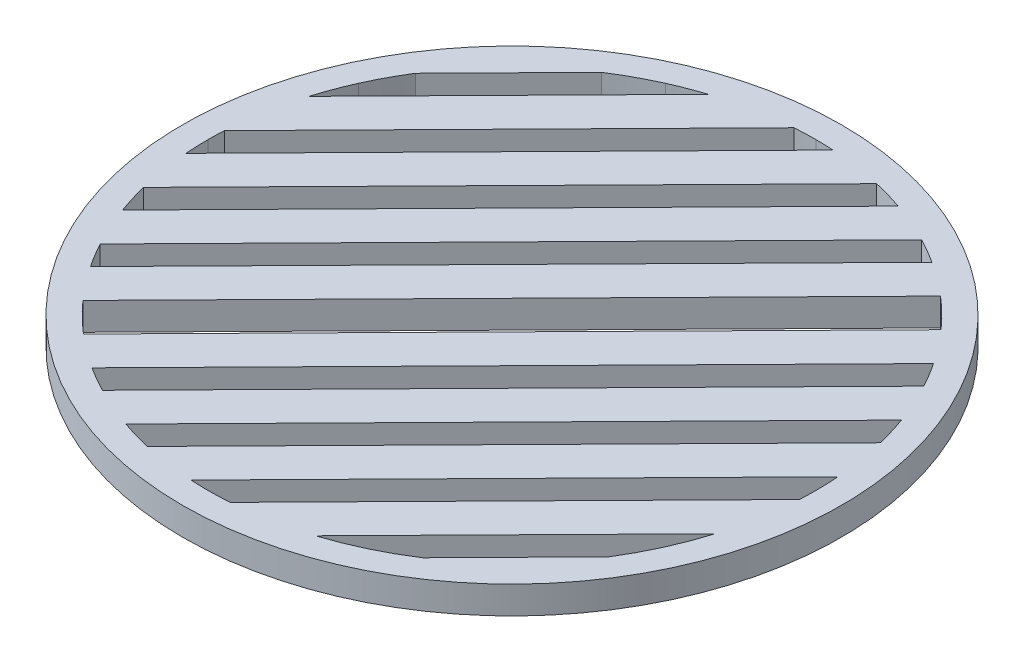
SolidWorks part; units mm, degrees
ref_plane "Front Plane" through (0, 0, 0) normal (0, 0, 1) x (1, 0, 0)
ref_plane "Top Plane" through (0, 0, 0) normal (0, 1, 0) x (1, 0, 0)
ref_plane "Right Plane" through (0, 0, 0) normal (1, 0, 0) x (0, 0, -1)
sketch "Sketch1" plane through (0, 0, 0) normal (0, 1, 0) x (1, 0, 0)
  line L0 (0, 27.9559) -> (-27.9559, 0)
  line L1 (3.3863, 27.75) -> (-27.75, -3.3863)
  line L2 (7.8542, 26.8299) -> (-26.8299, -7.8542)
  line L3 (-27.2932, 6.0508) -> (-6.0508, 27.2932)
  line L4 (-11.4185, 25.5176) -> (-25.5176, 11.4185)
  line L5 (10.5182, 25.9017) -> (-25.9017, -10.5182)
  line L6 (-22.121, -17.0936) -> (17.0936, 22.121) construction
  line L7 (14.1279, 24.1233) -> (-24.1233, -14.1279)
  line L8 (-22.7084, -16.3052) -> (16.3052, 22.7084)
  circle A0 centre (0, 0) radius 30.315
  circle A1 centre (0, 0) radius 27.9559
  arc A2 (-27.9559, 0) -> (-27.75, -3.3863) centre (0, 0) ccw
  arc A3 (0, 27.9559) -> (3.3863, 27.75) centre (0, 0) cw
  arc A4 (-25.5176, 11.4185) -> (-27.2932, 6.0508) centre (0, 0) ccw
  arc A5 (-11.4185, 25.5176) -> (-6.0508, 27.2932) centre (0, 0) cw
  arc A6 (-26.8299, -7.8542) -> (-25.9017, -10.5182) centre (0, 0) ccw
  arc A7 (7.8542, 26.8299) -> (10.5182, 25.9017) centre (0, 0) cw
  arc A8 (-24.1233, -14.1279) -> (-22.7084, -16.3052) centre (0, 0) ccw
  arc A9 (14.1279, 24.1233) -> (16.3052, 22.7084) centre (0, 0) cw
  dimension "D1" = 60.63
  dimension "D2" = 2.54
  dimension "D3" = 3.81
  dimension "D4" = 2.54
  dimension "D5" = 3.81
  dimension "D6" = 2.54
  dimension "D7" = 3.81
  dimension "D8" = 2.54
extrude "Boss-Extrude1" add sketch "Sketch1" along normal blind 2.54 contours L6 A1 | L8 A1 L7 | L7 A1 L5 | L5 A1 L2 | L2 A1 L1 | L0 A1 L3 | L3 A1 L4 | A0
sketch "Sketch2" plane through (0, 2.54, 0) normal (0, 1, 0) x (1, 0, 0)
  line L0 (1.6215, 27.9088) -> (-27.876, -2.112)
  line L3 (12.8418, 24.8318) -> (-24.6021, -13.2765)
  line L4 (9.0806, 26.44) -> (-26.2762, -9.5441)
  line L5 (6.3021, 27.2363) -> (-27.1212, -6.78)
  line L6 (-1.9608, 27.887) -> (-27.9172, 1.4702)
  line L7 (-26.7622, 8.0818) -> (-8.5512, 26.616)
  line L8 (-23.7079, 14.8144) -> (-15.229, 23.4437)
  line L9 (18.1975, 21.2222) -> (-20.8989, -18.5679)
  line L10 (0, 0) -> (19.7678, 19.7678)
  line L11 (0, 0) -> (-19.5932, -19.9408)
  line L12 (15.1127, 23.5189) -> (-23.2495, -15.5239)
  line L13 (15.229, -23.4437) -> (23.7079, -14.8144)
  line L14 (8.5512, -26.616) -> (26.7622, -8.0818)
  line L15 (27.9172, -1.4702) -> (1.9608, -27.887)
  line L16 (27.876, 2.112) -> (-1.6215, -27.9088)
  line L17 (27.1212, 6.78) -> (-6.3021, -27.2363)
  line L18 (26.2762, 9.5441) -> (-9.0806, -26.44)
  line L19 (24.6021, 13.2765) -> (-12.8418, -24.8318)
  line L20 (23.2495, 15.5239) -> (-15.1127, -23.5189)
  line L21 (20.8989, 18.5679) -> (-18.1975, -21.2222)
  arc A2 (16.3052, 22.7084) -> (3.3863, 27.75) centre (0, 0) ccw construction
  arc A3 (-27.75, -3.3863) -> (-22.7084, -16.3052) centre (0, 0) ccw construction
  arc A9 (3.3863, 27.75) -> (0, 27.9559) centre (0, 0) ccw construction
  arc A10 (-27.9559, 0) -> (-27.75, -3.3863) centre (0, 0) ccw construction
  arc A11 (0, 27.9559) -> (-11.4185, 25.5176) centre (0, 0) ccw construction
  arc A12 (-25.5176, 11.4185) -> (-27.9559, 0) centre (0, 0) ccw construction
  arc A13 (-11.4185, 25.5176) -> (-25.5176, 11.4185) centre (0, 0) ccw construction
  arc A14 (-26.7622, 8.0818) -> (-27.9172, 1.4702) centre (0, 0) ccw
  arc A15 (-23.7079, 14.8144) -> (-15.229, 23.4437) centre (0, 0) cw
  arc A16 (-27.876, -2.112) -> (-27.1212, -6.78) centre (0, 0) ccw
  arc A17 (-26.2762, -9.5441) -> (-24.6021, -13.2765) centre (0, 0) ccw
  arc A19 (-8.5512, 26.616) -> (-1.9608, 27.887) centre (0, 0) cw
  arc A20 (1.6215, 27.9088) -> (6.3021, 27.2363) centre (0, 0) cw
  arc A21 (9.0806, 26.44) -> (12.8418, 24.8318) centre (0, 0) cw
  arc A23 (-22.121, -17.0936) -> (17.0936, 22.121) centre (0, 0) ccw construction
  arc A25 (-23.2495, -15.5239) -> (-20.8989, -18.5679) centre (0, 0) ccw
  arc A26 (15.1127, 23.5189) -> (18.1975, 21.2222) centre (0, 0) cw
  arc A27 (15.229, -23.4437) -> (23.7079, -14.8144) centre (0, 0) ccw
  arc A28 (8.5512, -26.616) -> (1.9608, -27.887) centre (0, 0) cw
  arc A29 (26.7622, -8.0818) -> (27.9172, -1.4702) centre (0, 0) ccw
  arc A30 (27.876, 2.112) -> (27.1212, 6.78) centre (0, 0) ccw
  arc A31 (-1.6215, -27.9088) -> (-6.3021, -27.2363) centre (0, 0) cw
  arc A32 (-9.0806, -26.44) -> (-12.8418, -24.8318) centre (0, 0) cw
  arc A33 (26.2762, 9.5441) -> (24.6021, 13.2765) centre (0, 0) ccw
  arc A34 (-15.1127, -23.5189) -> (-18.1975, -21.2222) centre (0, 0) cw
  arc A35 (23.2495, 15.5239) -> (20.8989, 18.5679) centre (0, 0) ccw
  arc M25 (17.0936, 22.121) -> (-22.121, -17.0936) centre (0, 0) cw
  arc M26 (-22.121, -17.0936) -> (-22.7084, -16.3052) centre (0, 0) cw
  arc M27 (-22.7084, -16.3052) -> (-27.75, -3.3863) centre (0, 0) cw
  arc M28 (-27.75, -3.3863) -> (-27.9559, 0) centre (0, 0) cw
  arc M29 (-27.9559, 0) -> (-25.5176, 11.4185) centre (0, 0) cw
  arc M30 (-25.5176, 11.4185) -> (-11.4185, 25.5176) centre (0, 0) cw
  arc M31 (-11.4185, 25.5176) -> (0, 27.9559) centre (0, 0) cw
  arc M32 (0, 27.9559) -> (3.3863, 27.75) centre (0, 0) cw
  arc M33 (3.3863, 27.75) -> (16.3052, 22.7084) centre (0, 0) cw
  arc M34 (16.3052, 22.7084) -> (17.0936, 22.121) centre (0, 0) cw
  dimension "D1" = 2.54
  dimension "D2" = 3.81
  dimension "D3" = 3.81
  dimension "D4" = 2.54
  dimension "D5" = 3.81
  dimension "D6" = 2.54
  dimension "D7" = 3.81
  dimension "D8" = 2.54
  dimension "D9" = 0.504
extrude "Boss-Extrude3" add sketch "Sketch2" against normal blind 2.54 contours L21 L20 M25 | L19 L18 M25 | L17 L16 M25 | L15 L14 M25 | L13 M25 | L12 L9 M33 M27 M26 M25 M34 | L4 L3 M33 M27 | L5 L0 M33 M32 M28 M27 | L7 L6 M29 M31 | L8 M30
